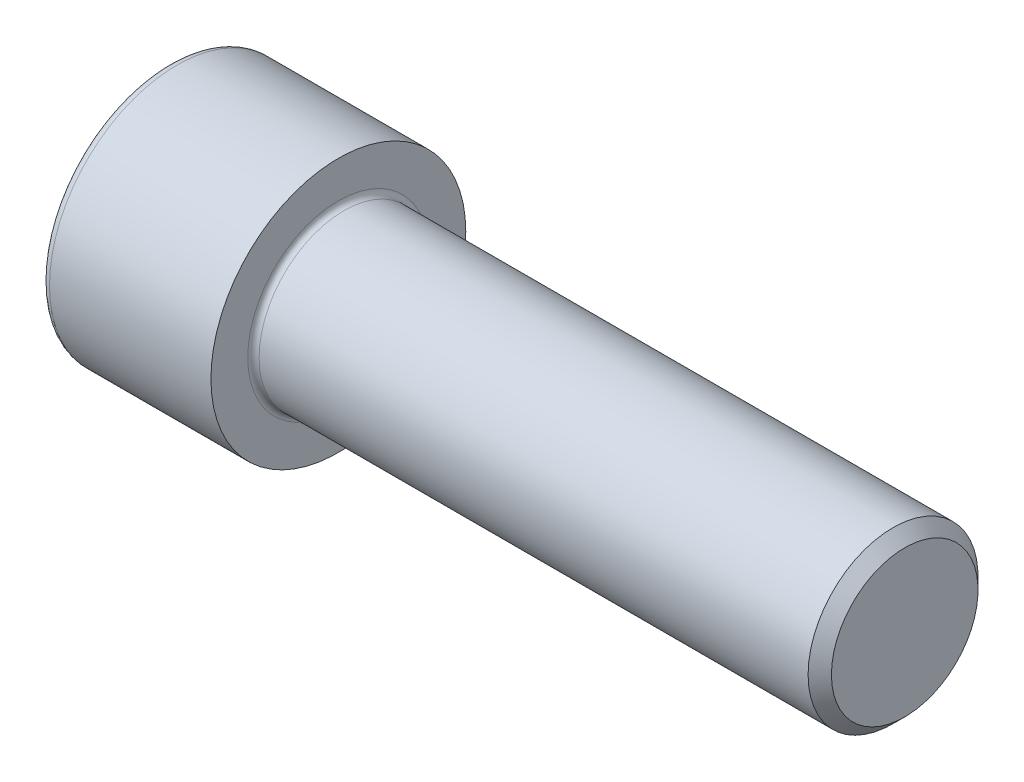
SolidWorks part; units mm, degrees
revolve "Base-Revolve" add sketch "BodySke"
sketch "BodySke" plane through (0, 0, 0) normal (0, 0, 1) x (1, 0, 0)
  line L0 (0, 0) -> (0, 18)
  line L1 (0, 18) -> (24, 18)
  line L2 (24, 18) -> (24, 12)
  line L3 (24, 12) -> (102.352, 12)
  line L4 (104, 10.352) -> (104, 0)
  line L5 (104, 0) -> (0, 0)
  line L6 (-31.75, 0) -> (127, 0) construction
  line L8 (104, 10.352) -> (102.352, 12)
  line L10 (104, -10.352) -> (102.352, -12) construction
  line L11 (27, 9.525) -> (27, 3.175) construction
  line L12 (44, 9.525) -> (44, 3.175) construction
  line L13 (44, 9.525) -> (44, 3.175) construction
  dimension "Length" = 80
  dimension "Body_ch_ang" = 45
  dimension "Thread_length" = 60
cosmetic thread "ThreadCosmetic" [suppressed]
fillet "Fillet1" radius 0.8 1 edges at (24, 0, 12)
fillet "Fillet2" radius 1.2 1 edges at (0, 0, 18)
ref_plane "Plane1" through (0, 0, 0) normal (0, 0, 1) x (1, 0, 0)
ref_plane "Plane2" through (0, 0, 0) normal (0, 1, 0) x (1, 0, 0)
ref_plane "Plane3" through (0, 0, 0) normal (1, 0, 0) x (0, 0, -1)
other "Configuration Table"
sketch "Sketch2" plane through (0, 0, 0) normal (0, 0, 1) x (1, 0, 0)
  line L0 (0, 9.6375) -> (12.573, 9.6375)
  line L1 (12.573, 9.6375) -> (18.1372, 0)
  line L2 (-31.75, 0) -> (127, 0) construction
  line L3 (18.1372, 0) -> (0, 0)
  line L4 (0, 0) -> (0, 9.6375)
  line L6 (0, 0) -> (47.625, 0) construction
  dimension "D2" = 60
revolve "Hex-PreBroach" cut sketch "Sketch2" angle 360 about L6
sketch "Sketch3" plane through (0, 0, 0) normal (-1, 0, 0) x (0, 0.5, 0.866)
  line L0 (5.5642, 9.6375) -> (-5.5642, 9.6375)
  line L1 (-5.5642, 9.6375) -> (-11.1284, 0)
  line L2 (5.5642, 9.6375) -> (11.1284, 0)
  line L3 (5.5642, -9.6375) -> (11.1284, 0)
  line L4 (5.5642, -9.6375) -> (-5.5642, -9.6375)
  line L5 (-5.5642, -9.6375) -> (-11.1284, 0)
extrude "Hex" cut sketch "Sketch3" against normal blind 12.573
sketch "ThdSchSke" plane through (0, 0, 0) normal (0, 0, 1) x (1, 0, 0)
  line L0 (44, -10.352) -> (42.8461, -12)
  line L1 (44, -10.352) -> (45.1539, -12)
  line L2 (45.1539, -12) -> (45.1539, -15)
  line L3 (-3.175, 0) -> (5.1513, 0) construction
  line L4 (0, 16.8) -> (0, -16.8) construction
  line L5 (45.1539, -15) -> (42.8461, -15)
  line L6 (42.8461, -15) -> (42.8461, -12)
revolve "ThreadSchematic" [suppressed] cut sketch "ThdSchSke" angle 360 about L3
pattern_linear "ThdSchPat" [suppressed]
equation "\"D2@Sketch3\" = \"Hex_size@Sketch3\" / 2"
equation "\"D1@Sketch3\" = \"Hex_size@Sketch3\" / 2"
equation "\"D1@Sketch2\" = \"Hex_size@Sketch3\" / 2"
equation "\"Thread_minor@ThreadCosmetic\"  =  \"Minor_dia@BodySke\""
equation "\"Depth@Sketch2\" =  \"Key_eng@Hex\""
equation "\"Thread_length@ThreadCosmetic\" = ((sgn( (\"Length@BodySke\" - \"Advance@BodySke\" * 3.0) - \"Thread_nom@BodySke\" )-1)*( (\"Length@BodySke\" - \"Advance@BodySke\" * 3.0) - \"Thread_nom@BodySke\" ))/-2+ \"Thread_nom@BodySke\""
equation "\"Thread_minor@ThdSchSke\" = \"Minor_dia@BodySke\""
equation "\"Diameter@ThdSchSke\" = \"Diameter@BodySke\""
equation "\"Overcut@ThdSchSke\" = \"Diameter@BodySke\" * 1.25"
equation "\"Start@ThdSchSke\" = \"Head_ht@BodySke\" + \"Length@BodySke\" - \"Thread_length@ThreadCosmetic\"  '---Non-countersunk---"
equation "\"Num_threads@ThdSchPat\" = int( \"Thread_length@ThreadCosmetic\" / \"Advance@BodySke\" + 0.999 )  + 1"
equation "\"Advance@ThdSchPat\" = \"Thread_length@ThreadCosmetic\" /  (\"Num_threads@ThdSchPat\" - 1) 'relax it"
equation "\"Num_threads@ThdSchPat\" = \"Num_threads@ThdSchPat\" - sgn( \"Num_threads@ThdSchPat\" - 1) '---chamfered tips only---"
